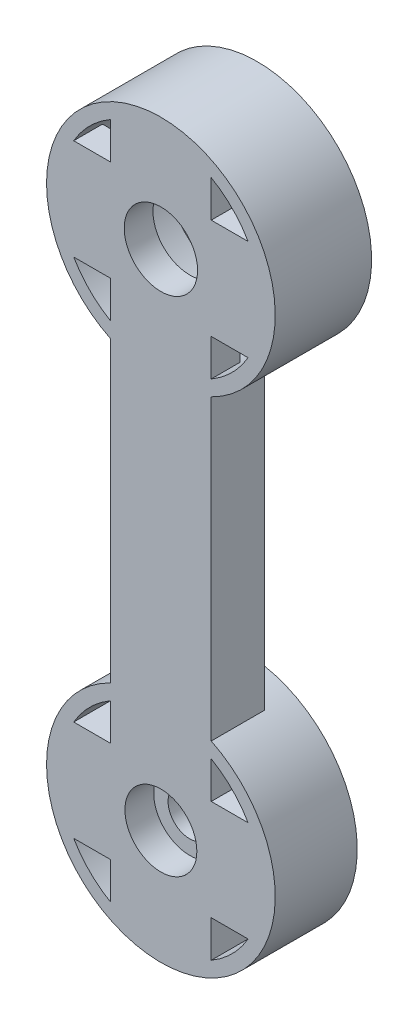
SolidWorks part; units mm, degrees
ref_plane "Front Plane" through (0, 0, 0) normal (0, 0, 1) x (1, 0, 0)
ref_plane "Top Plane" through (0, 0, 0) normal (0, 1, 0) x (1, 0, 0)
ref_plane "Right Plane" through (0, 0, 0) normal (1, 0, 0) x (0, 0, -1)
sketch "Sketch1" plane through (0, 0, 0) normal (0, 0, 1) x (1, 0, 0)
  line L5 (0, -17.5) -> (12.7696, -17.5) construction
  line L26 (0, 0) -> (0, -35) construction
  line L32 (0, 3.5) -> (7.1381, 3.5)
  line L33 (7.1381, 3.5) -> (-7.1381, 3.5)
  line L34 (0, -3.5) -> (7.1381, -3.5)
  line L35 (7.1381, -3.5) -> (-7.1381, -3.5)
  line L36 (3.5, -35) -> (3.5, -41.0622)
  line L37 (-3.5, -35) -> (-3.5, -41.0622)
  line L38 (-3.5, 0) -> (-3.5, 6.0622)
  line L45 (-3.5, 0) -> (-3.5, -35)
  line L47 (3.5, 0) -> (3.5, -35)
  line L48 (3.5, 0) -> (3.5, 6.0622)
  line L49 (7.1381, -31.5) -> (-7.1381, -31.5)
  line L50 (0, -31.5) -> (7.1381, -31.5)
  line L51 (7.1381, -38.5) -> (-7.1381, -38.5)
  line L52 (0, -38.5) -> (7.1381, -38.5)
  circle A0 centre (0, 0) radius 7.95
  circle A1 centre (0, 0) radius 3.5
  circle A2 centre (0, 0) radius 7
  circle A6 centre (0, 0) radius 1.5
  circle A11 centre (0, -35) radius 1.5
  circle A12 centre (0, -35) radius 7
  circle A13 centre (0, -35) radius 3.5
  circle A14 centre (0, -35) radius 7.95
  point P20 (0, -35)
  point P34 (0, -35)
  point P42 (0, 0)
  dimension "D1" = 15.9
  dimension "D2" = 7
  dimension "D6" = 14
  dimension "D9" = 3
  dimension "D3" = 7
  dimension "D7" = 35
extrude "Boss-Extrude4" add sketch "Sketch1" along normal blind 3 contours L48 A2 L38 L33 L32 | A2 L32 A0 L33 | L45 A14 L47 A0 | A14 L51 A12 | A12 L36 L51 L37 | A14 L49 A12 L51 | L36 A13 L51 | L51 A13 L37 | A14 L51 A12 L49 | A13 A11 | L45 A13 L49 | L49 A13 L47 | A12 L45 L49 L47 | A14 L49 A12 L45 | A14 L47 A12 L49 | A14 L45 A12 L47 | A12 L51 L37 L45 L49 | A12 L50 L47 L36 L52 | L45 A2 L47 L34 L35 | A2 L45 A0 L47 | A2 L47 A0 L34 | A2 L34 A0 L32 | A2 L33 A0 L35 | A2 L35 A0 L45 | L33 A2 L35 L45 L38 | L35 A2 L33 L48 L47 | A1 L34 L47 | A1 A6 | A1 L45 L35 | A1 L33 L38 | A1 L48 L32
sketch "Sketch3" plane through (0, 0, 0) normal (0, 0, -1) x (-1, 0, 0)
  line L0 (-3.5, 6.0622) -> (-3.5, 3.5)
  line L1 (-3.5, 3.5) -> (-6.0622, 3.5)
  line L2 (-3.5, -6.0622) -> (-3.5, -3.5)
  line L3 (-3.5, -3.5) -> (-6.0622, -3.5)
  line L4 (3.5, -6.0622) -> (3.5, -3.5)
  line L5 (3.5, -3.5) -> (6.0622, -3.5)
  line L6 (3.5, 6.0622) -> (3.5, 3.5)
  line L7 (3.5, 3.5) -> (6.0622, 3.5)
  line L8 (0, 0) -> (0, -35) construction
  line L9 (0, -35) -> (0, -17.5) construction
  line L10 (0, -17.5) -> (14.5774, -17.5) construction
  line L11 (-3.5, 3.5) -> (-6.0622, 3.5)
  line L12 (-3.5, 6.0622) -> (-3.5, 3.5)
  line L13 (-3.5, -3.5) -> (-6.0622, -3.5)
  line L14 (-3.5, -6.0622) -> (-3.5, -3.5)
  line L15 (3.5, -3.5) -> (6.0622, -3.5)
  line L16 (3.5, -6.0622) -> (3.5, -3.5)
  line L17 (3.5, 3.5) -> (6.0622, 3.5)
  line L18 (3.5, 6.0622) -> (3.5, 3.5)
  line L19 (3.5, -41.0622) -> (3.5, -38.5)
  line L20 (3.5, -38.5) -> (6.0622, -38.5)
  line L21 (3.5, -28.9378) -> (3.5, -31.5)
  line L22 (3.5, -31.5) -> (6.0622, -31.5)
  line L23 (-3.5, -28.9378) -> (-3.5, -31.5)
  line L24 (-3.5, -31.5) -> (-6.0622, -31.5)
  line L25 (-3.5, -41.0622) -> (-3.5, -38.5)
  line L26 (-3.5, -38.5) -> (-6.0622, -38.5)
  line L27 (3.5, -38.5) -> (6.0622, -38.5)
  line L28 (3.5, -41.0622) -> (3.5, -38.5)
  line L29 (3.5, -31.5) -> (6.0622, -31.5)
  line L30 (3.5, -28.9378) -> (3.5, -31.5)
  line L31 (-3.5, -31.5) -> (-6.0622, -31.5)
  line L32 (-3.5, -28.9378) -> (-3.5, -31.5)
  line L33 (-3.5, -38.5) -> (-6.0622, -38.5)
  line L34 (-3.5, -41.0622) -> (-3.5, -38.5)
  circle A0 centre (0, 0) radius 1.5
  circle A1 centre (0, 0) radius 7.95
  circle A2 centre (0, 0) radius 7
  circle A3 centre (0, -35) radius 7
  circle A4 centre (0, -35) radius 7.95
  circle A5 centre (0, -35) radius 1.5
  line M2 (3.5, -38.5) -> (6.0622, -38.5)
  arc M3 (6.0622, -38.5) -> (3.5, -41.0622) centre (0, -35) cw
  line M4 (3.5, -41.0622) -> (3.5, -38.5)
  line M5 (-3.5, -38.5) -> (-3.5, -41.0622)
  arc M6 (-3.5, -41.0622) -> (-6.0622, -38.5) centre (0, -35) cw
  line M7 (-6.0622, -38.5) -> (-3.5, -38.5)
  arc M9 (3.5, -7.1381) -> (-3.5, -7.1381) centre (0, 0) ccw
  arc M11 (-3.5, -27.8619) -> (3.5, -27.8619) centre (0, -35) ccw
  line M12 (6.0622, -31.5) -> (3.5, -31.5)
  line M13 (3.5, -31.5) -> (3.5, -28.9378)
  arc M14 (3.5, -28.9378) -> (6.0622, -31.5) centre (0, -35) cw
  arc M15 (-3.5, -6.0622) -> (-6.0622, -3.5) centre (0, 0) cw
  line M16 (-6.0622, -3.5) -> (-3.5, -3.5)
  line M17 (-3.5, -3.5) -> (-3.5, -6.0622)
  line M18 (-3.5, -31.5) -> (-6.0622, -31.5)
  arc M19 (-6.0622, -31.5) -> (-3.5, -28.9378) centre (0, -35) cw
  line M20 (-3.5, -28.9378) -> (-3.5, -31.5)
  line M21 (3.5, -3.5) -> (6.0622, -3.5)
  arc M22 (6.0622, -3.5) -> (3.5, -6.0622) centre (0, 0) cw
  line M23 (3.5, -6.0622) -> (3.5, -3.5)
  line M24 (6.0622, 3.5) -> (3.5, 3.5)
  line M25 (3.5, 3.5) -> (3.5, 6.0622)
  arc M26 (3.5, 6.0622) -> (6.0622, 3.5) centre (0, 0) cw
  arc M27 (-6.0622, 3.5) -> (-3.5, 6.0622) centre (0, 0) cw
  line M28 (-3.5, 6.0622) -> (-3.5, 3.5)
  line M29 (-3.5, 3.5) -> (-6.0622, 3.5)
  circle M30 centre (0, 0) radius 1.5
  circle M31 centre (0, -35) radius 1.5
  dimension "D1" = 15.9
extrude "Boss-Extrude5" add sketch "Sketch3" along normal blind 3 contours A1 A2 M9 M26 M22 M15 M27 | A2 M25 M28 M29 M16 M17 M23 M21 M24 M30 | A3 M4 M2 M12 M13 M20 M18 M7 M5 M31 | A4 A3 M11 M3 M6 M19 M14
sketch "Sketch4" plane through (0, 0, 3) normal (0, 0, 1) x (1, 0, 0)
  line L0 (0, 0) -> (0, -35) construction
  line L1 (0, -35) -> (0, 0) construction
  line L2 (0, -17.5) -> (19.6941, -17.5) construction
  circle A1 centre (0, -35) radius 2.5
  circle A2 centre (0, 0) radius 2.5
  dimension "D2" = 5
extrude "Cut-Extrude1" cut sketch "Sketch4" against normal blind 1.5
sketch "Sketch5" plane through (0, 0, -3) normal (0, 0, -1) x (-1, 0, 0)
  circle A0 centre (0, 0) radius 7
extrude "Cut-Extrude2" cut sketch "Sketch5" against normal blind 4
sketch "Sketch6" plane through (0, 0, -3) normal (0, 0, -1) x (-1, 0, 0)
  circle A0 centre (0, -35) radius 7.95
extrude "Cut-Extrude3" cut sketch "Sketch6" against normal blind 1
sketch "Sketch7" plane through (0, 0, 1.5) normal (0, 0, 1) x (1, 0, 0)
  circle A0 centre (0, -35) radius 2.5
extrude "Cut-Extrude4" cut sketch "Sketch7" against normal blind 0.5
sketch "Sketch8" plane through (0, 0, -3) normal (0, 0, -1) x (-1, 0, 0)
  circle A0 centre (0, 0) radius 7.95
  circle A1 centre (0, 0) radius 7
extrude "Boss-Extrude6" add sketch "Sketch8" along normal blind 0.7
sketch "Sketch9" plane through (0, 0, -2) normal (0, 0, -1) x (-1, 0, 0)
  line L0 (-3.5, -28.9378) -> (-3.5, -31.5)
  line L1 (-3.5, -31.5) -> (-6.0622, -31.5)
  line L2 (-6.0622, -38.5) -> (-3.5, -38.5)
  line L3 (-3.5, -38.5) -> (-3.5, -41.0622)
  line L4 (6.0622, -38.5) -> (3.5, -38.5)
  line L5 (3.5, -38.5) -> (3.5, -41.0622)
  line L6 (3.5, -28.9378) -> (3.5, -31.5)
  line L7 (3.5, -31.5) -> (6.0622, -31.5)
  circle A0 centre (0, -35) radius 7.95
  circle A1 centre (0, -35) radius 7
  circle A2 centre (0, -35) radius 1.5
  line M1 (6.0622, -31.5) -> (3.5, -31.5)
  line M2 (3.5, -31.5) -> (3.5, -28.9378)
  arc M3 (3.5, -28.9378) -> (6.0622, -31.5) centre (0, -35) cw
  arc M4 (-3.5, -41.0622) -> (-6.0622, -38.5) centre (0, -35) cw
  line M5 (-6.0622, -38.5) -> (-3.5, -38.5)
  line M6 (-3.5, -38.5) -> (-3.5, -41.0622)
  arc M7 (6.0622, -38.5) -> (3.5, -41.0622) centre (0, -35) cw
  line M8 (3.5, -41.0622) -> (3.5, -38.5)
  line M9 (3.5, -38.5) -> (6.0622, -38.5)
  circle M10 centre (0, -35) radius 7.95
  line M11 (-3.5, -31.5) -> (-6.0622, -31.5)
  arc M12 (-6.0622, -31.5) -> (-3.5, -28.9378) centre (0, -35) cw
  line M13 (-3.5, -28.9378) -> (-3.5, -31.5)
  circle M14 centre (0, -35) radius 1.5
extrude "Boss-Extrude8" add sketch "Sketch9" along normal blind 0.7 contours A1 M2 M13 M11 M5 M6 M8 M9 M1 M14 | A1 M10 M3 M7 M4 M12 | A0
sketch "Sketch10" plane through (0, 0, 0) normal (0, 0, -1) x (-1, 0, 0)
  line L2 (-3.5, -7.1381) -> (-3.5, -27.8619)
  line L4 (3.5, -7.1381) -> (3.5, -27.8619)
  circle A0 centre (0, 0) radius 7.95
  circle A1 centre (0, -35) radius 7.95
  line M1 (-3.5, -7.1381) -> (-3.5, -27.8619)
  arc M2 (-3.5, -27.8619) -> (3.5, -27.8619) centre (0, -35) cw
  line M3 (3.5, -27.8619) -> (3.5, -7.1381)
  arc M4 (3.5, -7.1381) -> (-3.5, -7.1381) centre (0, 0) cw
extrude "Boss-Extrude9" add sketch "Sketch10" along normal blind 0.7 contours M4 M1 M2 M3
sketch "Sketch11" plane through (0, 0, 3) normal (0, 0, 1) x (1, 0, 0)
  circle A0 centre (0, 0) radius 2.55
  dimension "D1" = 5.1
extrude "Cut-Extrude5" cut sketch "Sketch11" against normal through all
